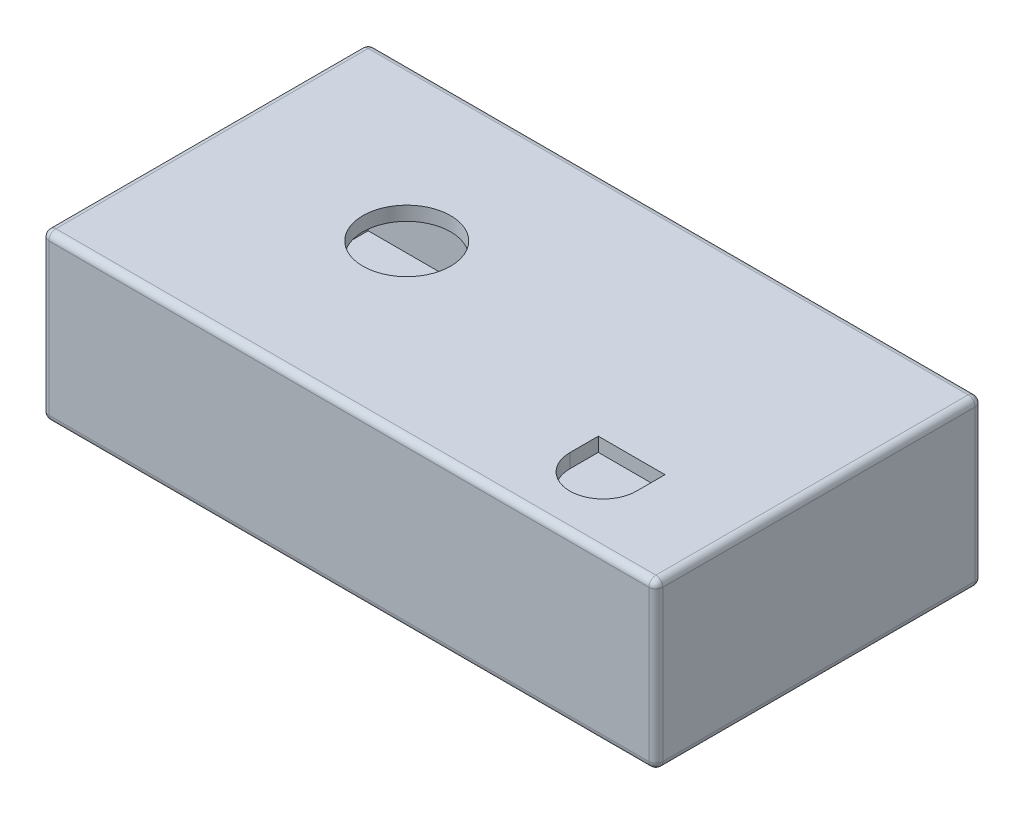
SolidWorks part; units mm, degrees
ref_plane "Front Plane" through (0, 0, 0) normal (0, 0, 1) x (1, 0, 0)
ref_plane "Top Plane" through (0, 0, 0) normal (0, 1, 0) x (1, 0, 0)
ref_plane "Right Plane" through (0, 0, 0) normal (1, 0, 0) x (0, 0, -1)
sketch "Sketch1" plane through (0, 0, 0) normal (0, 0, 1) x (1, 0, 0)
  line L1 (0, 0) -> (222.25, 0)
  line L2 (0, 0) -> (0, 59.69)
  line L3 (0, 59.69) -> (222.25, 59.69)
  line L4 (222.25, 0) -> (222.25, 59.69)
  dimension "D1" = 59.69
  dimension "D2" = 222.25
extrude "Boss-Extrude1" add sketch "Sketch1" along normal blind 118.11
fillet "Fillet1" radius 2.54 12 edges at (111.125, 0, 118.11) (222.25, 0, 59.055) (0, 0, 59.055) (111.125, 0, 0) (0, 29.845, 0) (222.25, 29.845, 0) (222.25, 29.845, 118.11) (0, 29.845, 118.11) (111.125, 59.69, 118.11) (222.25, 59.69, 59.055) (111.125, 59.69, 0) (0, 59.69, 59.055)
shell "Shell1" thickness 5.08
sketch "Sketch2" plane through (0, 59.69, 0) normal (0, 1, 0) x (1, 0, 0)
  line L0 (2.54, 0) -> (219.71, 0) construction
  line L1 (222.25, -2.54) -> (222.25, -115.57) construction
  line L4 (165.735, -82.423) -> (189.865, -82.423)
  line L5 (189.865, -82.423) -> (189.865, -92.71)
  line L6 (165.735, -92.71) -> (165.735, -82.423)
  line L7 (219.71, -118.11) -> (2.54, -118.11) construction
  circle A0 centre (69.85, -55.88) radius 15.875
  arc A1 (189.865, -92.71) -> (165.735, -92.71) centre (177.8, -92.71) cw
  point P11 (189.865, -87.5665)
  point P12 (177.8, -104.775)
  point P17 (219.71, -90.4481)
  dimension "D1" = 31.75
  dimension "D6" = 25.4
  dimension "D2" = 55.88
  dimension "D3" = 152.4
  dimension "D4" = 24.13
  dimension "D5" = 22.352
  dimension "D7" = 44.45
extrude "Cut-Extrude1" cut sketch "Sketch2" against normal blind 7.62
